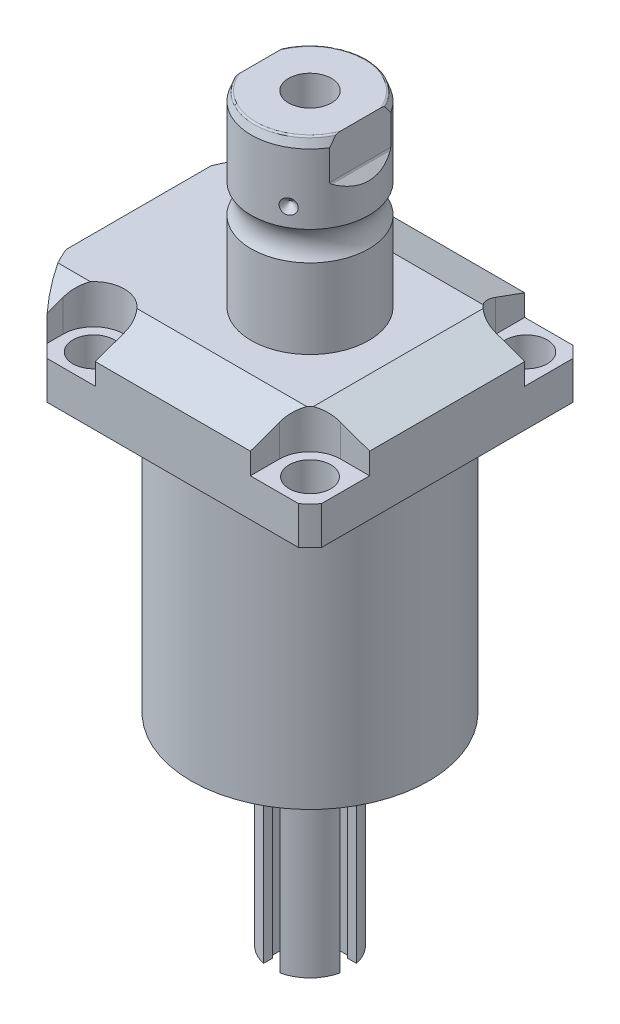
SolidWorks part; units mm, degrees
material "Alloy Steel"
ref_plane "Front Plane" through (0, 0, 0) normal (0, 0, 1) x (1, 0, 0)
ref_plane "Top Plane" through (0, 0, 0) normal (0, 1, 0) x (1, 0, 0)
ref_plane "Right Plane" through (0, 0, 0) normal (1, 0, 0) x (0, 0, -1)
ref_plane "Plane1" through (0, 0, 0) normal (0, 1, 0) x (0, 0, 1)
sketch "Sketch1" plane through (0, 0, 0) normal (0, 1, 0) x (0, 0, 1)
  line L0 (-44.45, 44.45) -> (44.45, 44.45)
  line L1 (44.45, 44.45) -> (44.45, -55.55)
  line L2 (44.45, -55.55) -> (-44.45, -55.55)
  line L3 (-44.45, -55.55) -> (-44.45, 44.45)
  line L4 (0, 0) -> (0, -60.6467) construction
  dimension "D1" = 55.55
  dimension "D2" = 100
  dimension "D3" = 88.9
extrude "Extrude1" add sketch "Sketch1" along normal blind 113.919
sketch "Sketch2" plane through (0, 0, 0) normal (0, -1, 0) x (1, 0, 0)
  circle A0 centre (0, 0) radius 60.325
  dimension "D1" = 120.65
extrude "Cut-Extrude1" cut sketch "Sketch2" against normal through all flip side to cut
ref_plane "Plane2" through (0, 0, 0) normal (1, 0, 0) x (0, 0, 1)
sketch "Sketch3" plane through (0, 0, 0) normal (1, 0, 0) x (0, 0, 1)
  line L0 (38.4935, 0) -> (38.4935, -88.9)
  line L1 (38.4935, -88.9) -> (76.5937, -88.9)
  line L2 (76.5937, -88.9) -> (76.5937, 0)
  line L3 (76.5937, 0) -> (38.4935, 0)
  line L4 (0, -93.345) -> (0, 4.445) construction
  line L5 (40.7836, 0) -> (-40.7836, 0) construction
  dimension "D1" = 76.987
  dimension "D2" = 153.1874
  dimension "D3" = 88.9
revolve "Cut-Revolve1" cut sketch "Sketch3" angle 360 about L4
fillet "Fillet1" radius 0.381 1 edges at (0, 88.9, 38.4935)
sketch "Sketch4" plane through (0, 113.919, 0) normal (0, 1, 0) x (-1, 0, 0)
  line L0 (-44.45, 40.7836) -> (-44.45, -40.7836) construction
  line L1 (40.7836, 44.45) -> (-40.7836, 44.45) construction
  line L2 (-25.121, -44.45) -> (-25.121, -35.052)
  line L3 (-44.45, -44.45) -> (-25.121, -44.45)
  line L4 (-44.45, -25.121) -> (-44.45, -44.45)
  line L5 (-35.052, -25.121) -> (-44.45, -25.121)
  line L6 (44.983, -44.45) -> (25.121, -44.45)
  line L7 (25.121, 44.45) -> (25.121, 35.052)
  line L8 (44.983, 44.45) -> (44.983, 35.052)
  line L9 (44.983, 44.45) -> (25.121, 44.45)
  line L10 (-35.052, 25.121) -> (-44.45, 25.121)
  line L11 (-44.45, 25.121) -> (-44.45, 44.45)
  line L12 (-44.45, 44.45) -> (-25.121, 44.45)
  line L13 (-25.121, 44.45) -> (-25.121, 35.052)
  line L14 (-48.9217, 0) -> (49.4551, 0) construction
  line L15 (44.983, -44.45) -> (44.983, -35.052)
  line L16 (25.121, -44.45) -> (25.121, -35.052)
  arc A0 (25.121, -35.052) -> (44.983, -35.052) centre (35.052, -35.052) cw
  arc A1 (-35.052, -25.121) -> (-25.121, -35.052) centre (-35.052, -35.052) cw
  arc A2 (-35.052, 25.121) -> (-25.121, 35.052) centre (-35.052, 35.052) ccw
  arc A3 (25.121, 35.052) -> (44.983, 35.052) centre (35.052, 35.052) ccw
  dimension "D2" = 9.931
  dimension "D1" = 35.052
  dimension "D3" = 35.052
  dimension "D4" = 35.052
extrude "Cut-Extrude2" cut sketch "Sketch4" against normal blind 12.7
ref_plane "Plane3" through (0, 0, 0) normal (1, 0, 0) x (0, 0, -1)
sketch "Sketch5" plane through (0, 0, 0) normal (1, 0, 0) x (0, 0, -1)
  line L0 (-28.575, 113.919) -> (-44.45, 108.141)
  line L1 (0, 0) -> (0, 154.1081) construction
  line L2 (-28.575, 113.919) -> (-44.45, 113.919)
  line L3 (-44.45, 113.919) -> (-44.45, 108.141)
  dimension "D1" = 15.875
  dimension "D2" = 20
extrude "Cut-Extrude9" cut sketch "Sketch5" against normal through all and the other way through all
mirror "Mirror1" about plane through (0, 0, 0) normal (0, 0, 1) of "Cut-Extrude9"
ref_plane "Plane7" through (0, 0, 0) normal (0, 0, 1) x (1, 0, 0)
sketch "Sketch9" plane through (0, 0, 0) normal (0, 0, 1) x (1, 0, 0)
  line L0 (28.575, 113.919) -> (44.45, 108.141)
  line L1 (44.45, 108.141) -> (44.45, 113.919)
  line L2 (44.45, 113.919) -> (28.575, 113.919)
  dimension "D1" = 15.875
  dimension "D2" = 20
extrude "Cut-Extrude7" cut sketch "Sketch9" against normal through all and the other way through all
ref_plane "Plane8" through (-41.402, 88.9, -18.1102) normal (1, 0, 0) x (0, 1, 0)
sketch "Sketch20" plane through (-41.402, 88.9, -18.1102) normal (1, 0, 0) x (0, 1, 0)
  line L0 (-88.9, 18.1102) -> (39.8401, 18.1102) construction
  line L1 (-7.2797, 36.2202) -> (36.9042, 36.2202) construction
  line L2 (0, 41.9225) -> (1.4478, 41.9225)
  line L3 (0, 58.8938) -> (0, -22.6734) construction
  line L4 (1.4478, 41.9225) -> (1.4478, 39.4714)
  line L5 (1.4478, 39.4714) -> (2.4638, 39.4714)
  line L6 (2.4638, 39.4714) -> (2.4638, 37.4648)
  line L7 (2.4638, 37.4648) -> (13.4366, 37.4648)
  line L8 (13.4366, 37.4648) -> (13.4366, 36.2202)
  line L9 (13.4366, 36.2202) -> (0, 36.2202)
  line L10 (0, 41.9225) -> (0, 36.2202)
  dimension "D1" = 18.11
  dimension "D2" = 11.4046
  dimension "D3" = 1.4478
  dimension "D4" = 6.5024
  dimension "D5" = 1.016
  dimension "D6" = 2.4892
  dimension "D7" = 10.9728
revolve "Cut-Revolve4" cut sketch "Sketch20" angle 360 about L1
mirror "Mirror10" about plane through (0, 0, 0) normal (0, 0, 1) of "Cut-Revolve4"
sketch "Sketch10" plane through (-41.402, 88.9, -18.1102) normal (1, 0, 0) x (0, 1, 0)
  line L0 (-1.0325, 0.0002) -> (1.5659, 0.0002) construction
  line L1 (13.4366, 1.2448) -> (2.4638, 1.2448) construction
  line L2 (2.4638, -1.2444) -> (13.4366, -1.2444) construction
  line L3 (0, 58.8938) -> (0, -22.6734) construction
  circle A0 centre (0.2667, 4.5214) radius 1.1811
  dimension "D1" = 2.3622
  dimension "D2" = 0.2667
  dimension "D3" = 9.0424
revolve "Revolve4" add sketch "Sketch10" angle 360 about L0
ref_plane "Plane9" through (-41.402, 88.9, 18.1102) normal (1, 0, 0) x (0, 1, 0)
sketch "Sketch11" plane through (-41.402, 88.9, 18.1102) normal (1, 0, 0) x (0, 1, 0)
  line L0 (-1.0325, -0.0002) -> (1.5659, -0.0002) construction
  line L1 (13.4366, 1.2444) -> (2.4638, 1.2444) construction
  line L3 (0, 22.6734) -> (0, -58.8938) construction
  line L4 (2.4638, -1.2448) -> (13.4366, -1.2448) construction
  circle A0 centre (0.2667, 4.521) radius 1.1811
  dimension "D1" = 2.3622
  dimension "D2" = 9.0424
  dimension "D3" = 0.2667
revolve "Revolve2" add sketch "Sketch11" angle 360 about L0
ref_plane "Plane10" through (-55.5498, 101.9048, 12.9794) normal (0, 0, 1) x (0, 1, 0)
sketch "S2D0007" plane through (-55.5498, 101.9048, 12.9794) normal (0, 0, 1) x (0, 1, 0)
  line L0 (0.0002, 0.0002) -> (10.7444, 0.0002)
  line L1 (10.7444, 0.0002) -> (10.7444, -0.2538)
  line L2 (10.7444, -0.2538) -> (6.655, -0.2538)
  line L3 (6.655, -0.2538) -> (5.9438, -0.965)
  line L5 (5.9438, -0.965) -> (5.9438, -14.427)
  line L6 (5.9438, -14.427) -> (0.0002, -14.427)
  line L7 (0.0002, -14.427) -> (0.0002, 0.0002)
  line L8 (0.0002, -14.9352) -> (0.0002, 0.7112) construction
  line L9 (-13.0048, 0.0002) -> (-13.0048, -14.7662) construction
  line L10 (12.0142, 0.0002) -> (-13.0048, 0.0002) construction
  dimension "D1" = 0.254
  dimension "D2" = 13.005
  dimension "D3" = 45
  dimension "D4" = 0.254
  dimension "D5" = 21.4884
  dimension "D6" = 13.3096
  dimension "D9" = 11.8872
  dimension "D10" = 14.1732
revolve "Cut-Revolve2" cut sketch "S2D0007" angle 360 about L8
pattern_linear "LPattern1" count 2 spacing 25.9588 along (0, 0, -1) of "Cut-Revolve2"
ref_plane "Plane12" through (0, 0, 0) normal (1, 0, 0) x (0, -1, 0)
sketch "Sketch15" plane through (0, 0, 0) normal (1, 0, 0) x (0, -1, 0)
  line L0 (-113.919, 0) -> (-113.919, 19.05)
  line L1 (-113.919, 19.05) -> (-139.6407, 19.05)
  line L2 (-149.0553, 19.05) -> (-171.602, 19.05)
  line L3 (-174.523, 17.9868) -> (-174.523, 0)
  line L4 (-174.523, 0) -> (-113.919, 0)
  line L5 (-197.6361, 0) -> (-64.6704, 0) construction
  line L6 (-113.919, 27.5238) -> (-113.919, -27.5238) construction
  line L8 (-174.523, 17.9868) -> (-171.602, 19.05)
  line L9 (0, -38.4935) -> (0, 38.4935) construction
  arc A0 (-149.0553, 19.05) -> (-139.6407, 19.05) centre (-144.348, 25.4255) ccw
  dimension "D2" = 20
  dimension "D4" = 7.925
  dimension "D6" = 35.001
  dimension "D1" = 174.523
  dimension "D3" = 38.1
  dimension "D5" = 30.175
  dimension "D7" = 2.921
revolve "Revolve3" add sketch "Sketch15" angle 360 about L5
ref_plane "Plane13" through (0, 0, 0) normal (0, 0, -1) x (0, -1, 0)
sketch "Sketch16" plane through (0, 0, 0) normal (0, 0, 1) x (0, -1, 0)
  line L0 (-174.523, 19.05) -> (-158.7389, 19.05)
  line L1 (-174.523, -19.05) -> (-174.523, -16.2815)
  line L2 (-174.523, 16.2815) -> (-161.823, 16.2815)
  line L3 (-161.2842, 16.5047) -> (-158.7389, 19.05)
  line L4 (-161.2842, -16.5047) -> (-158.7389, -19.05)
  line L5 (-174.523, -16.2815) -> (-161.823, -16.2815)
  line L6 (-174.523, 19.05) -> (-174.523, 16.2815)
  line L7 (-174.523, -19.05) -> (-158.7389, -19.05)
  line L8 (-194.0458, 0) -> (-125.0021, 0) construction
  line L11 (-174.523, 17.9868) -> (-174.523, -17.9868) construction
  line L12 (-149.0553, 19.05) -> (-171.602, 19.05) construction
  arc A0 (-161.823, 16.2815) -> (-161.2842, 16.5047) centre (-161.823, 17.0435) ccw
  arc A1 (-161.823, -16.2815) -> (-161.2842, -16.5047) centre (-161.823, -17.0435) cw
  point P3 (-161.5074, 16.2815)
  dimension "D4" = 0.762
  dimension "D1" = 32.563
  dimension "D2" = 45
  dimension "D3" = 12.7
extrude "Cut-Extrude8" cut sketch "Sketch16" against normal mid plane 106.68
hole_wizard "Hole1" positions "Sketch18" profile "Sketch17" legacy end condition up to next
sketch "Sketch18" plane through (0, 101.219, 0) normal (0, 1, 0) x (-1, 0, 0)
  arc A0 (44.983, -35.052) -> (25.121, -35.052) centre (35.052, -35.052) ccw construction
  arc A1 (25.121, 35.052) -> (44.983, 35.052) centre (35.052, 35.052) ccw construction
  arc A2 (-35.052, 25.121) -> (-25.121, 35.052) centre (-35.052, 35.052) ccw construction
  arc A3 (-25.121, -35.052) -> (-35.052, -25.121) centre (-35.052, -35.052) ccw construction
  point P0 (-35.052, -35.052)
  point P1 (-35.052, 35.052)
  point P3 (35.052, 35.052)
  point P5 (35.052, -35.052)
sketch "Sketch17" plane through (35.052, 101.219, -35.052) normal (1, 0, 0) x (0, 0, 1)
  line L0 (0, 0) -> (0, 12.319)
  line L1 (0, 12.319) -> (6.7435, 12.319)
  line L2 (6.7435, 12.319) -> (6.7435, 0)
  line L3 (6.7435, 0) -> (0, 0)
  line L4 (0, 110) -> (0, -10) construction
  dimension "Diameter" = 13.487
  dimension "Depth" = 12.319
chamfer "Chamfer1" distance 0.635 angle 45 2 edges at (-41.402, 91.3638, 16.8654) (-41.402, 91.3638, -16.8654)
sketch "Sketch21" plane through (0, 0, 0) normal (0, 0, 1) x (1, 0, 0)
  line L0 (0, 0) -> (0, 194.0957) construction
  line L1 (0, 144.9565) -> (6.9342, 149.123)
  line L2 (6.9342, 149.123) -> (6.9342, 174.523)
  line L4 (6.9342, 174.523) -> (0, 174.523)
  line L5 (0, 174.523) -> (0, 144.9565)
  line L6 (16.2815, 174.523) -> (-16.2815, 174.523) construction
  dimension "D1" = 13.8684
  dimension "D2" = 59
  dimension "D3" = 25.4
revolve "Cut-Revolve5" cut sketch "Sketch21" angle 360 about L0
fillet "Fillet2" radius 0.635 2 edges at (0, 174.523, -17.9868) (0, 174.523, 17.9868)
sketch "Sketch22" plane through (0, 0, 0) normal (0, 0, 1) x (1, 0, 0)
  line L0 (-37.9974, 155.016) -> (37.12, 155.016) construction
  line L1 (-19.05, 157.429) -> (-16.637, 155.016)
  line L2 (-16.637, 155.016) -> (-19.05, 155.016)
  line L3 (-19.05, 155.016) -> (-19.05, 157.429)
  arc A0 (-19.05, 139.6407) -> (-19.05, 149.0553) centre (-25.4255, 144.348) ccw construction
  dimension "D2" = 10.668
  dimension "D1" = 4.826
  dimension "D3" = 45
revolve "Cut-Revolve6" cut sketch "Sketch22" angle 360 about L0
pattern_circular "CirPattern1" count 3 over 360 about axis through (0, 197.6361, 0) along (0, 1, 0) of "Cut-Revolve6"
sketch "Sketch23" plane through (0, 0, 0) normal (0, 0, 1) x (1, 0, 0)
  line L0 (0, -970.2435) -> (0, 49029.7565) construction
  line L2 (0, 0) -> (-22.225, 0)
  line L3 (-38.4935, 0) -> (38.4935, 0) construction
  line L4 (-22.225, 0) -> (-22.225, -2.54)
  line L5 (-22.225, -2.54) -> (-12.7, -2.54)
  line L6 (-12.7, -2.54) -> (-12.7, -65.5321)
  line L7 (-12.7, -65.5321) -> (0, -65.5321)
  line L8 (0, -65.5321) -> (0, 0)
  dimension "D1" = 25.4001
  dimension "D2" = 65.5321
  dimension "D3" = 2.54
  dimension "D4" = 44.4501
revolve "Revolve5" add sketch "Sketch23" angle 360 about L0
sketch "Sketch24" plane through (0, -2.54, 0) normal (0, -1, 0) x (1, 0, 0)
  line L0 (-1000, 0) -> (49000, 0) construction
  line L2 (0, -1000) -> (0, 49000) construction
  line L3 (0, 0) -> (43301.2702, 25000) construction
  line L4 (0, 0) -> (25000, 43301.2702) construction
  circle A0 centre (0, 0) radius 19.431 construction
  circle A1 centre (19.431, 0) radius 1.7272
  circle A2 centre (16.8278, 9.7155) radius 1.7272
  circle A3 centre (9.7155, 16.8278) radius 1.7272
  circle A4 centre (0, 19.431) radius 1.7272
  circle A5 centre (-9.7155, 16.8278) radius 1.7272
  circle A6 centre (-16.8278, 9.7155) radius 1.7272
  circle A7 centre (-19.431, 0) radius 1.7272
  circle A8 centre (16.8278, -9.7155) radius 1.7272
  circle A9 centre (9.7155, -16.8278) radius 1.7272
  circle A10 centre (0, -19.431) radius 1.7272
  circle A11 centre (-9.7155, -16.8278) radius 1.7272
  circle A12 centre (-16.8278, -9.7155) radius 1.7272
  dimension "D3" = 38.8621
  dimension "D4" = 3.4544
  dimension "D5" = 3.4544
  dimension "D6" = 3.4544
  dimension "D7" = 3.4544
  dimension "D1" = 30
  dimension "D2" = 30
extrude "Cut-Extrude10" cut sketch "Sketch24" against normal up to surface (2.54 mm away) up to face at (0, 0, 38.4935)
sketch "Sketch25" plane through (0, -2.54, 0) normal (0, -1, 0) x (1, 0, 0)
  circle A0 centre (19.431, 0) radius 2.7051
  circle A1 centre (-9.7155, 16.8278) radius 2.7051
  circle A2 centre (-9.7155, -16.8278) radius 2.7051
  dimension "D1" = 5.4102
  dimension "D2" = 5.4102
  dimension "D3" = 5.4102
extrude "Extrude2" add sketch "Sketch25" along normal blind 2.9464
sketch "Sketch26" plane through (0, -5.4864, 0) normal (0, -1, 0) x (1, 0, 0)
  line L1 (-9.0153, -18.09) -> (-8.2724, -16.8525)
  line L2 (-8.2724, -16.8525) -> (-8.9725, -15.5903)
  line L3 (-8.9725, -15.5903) -> (-10.4157, -15.5656)
  line L4 (-10.4157, -15.5656) -> (-11.1587, -16.8031)
  line L5 (-11.1587, -16.8031) -> (-10.4585, -18.0652)
  line L6 (-10.4585, -18.0652) -> (-9.0153, -18.09)
  line L7 (19.9976, -1.3275) -> (20.864, -0.1731)
  line L8 (20.864, -0.1731) -> (20.2974, 1.1545)
  line L9 (20.2974, 1.1545) -> (18.8644, 1.3275)
  line L10 (18.8644, 1.3275) -> (17.9981, 0.1731)
  line L11 (17.9981, 0.1731) -> (18.5647, -1.1545)
  line L12 (18.5647, -1.1545) -> (19.9976, -1.3275)
  line L13 (-9.0392, 15.5527) -> (-8.2731, 16.776)
  line L14 (-8.2731, 16.776) -> (-8.9494, 18.0511)
  line L15 (-8.9494, 18.0511) -> (-10.3919, 18.1029)
  line L16 (-10.3919, 18.1029) -> (-11.158, 16.8796)
  line L17 (-11.158, 16.8796) -> (-10.4816, 15.6045)
  line L18 (-10.4816, 15.6045) -> (-9.0392, 15.5527)
  circle A0 centre (-9.7155, -16.8278) radius 1.25 construction
  circle A1 centre (19.431, 0) radius 1.25 construction
  circle A2 centre (-9.7155, 16.8278) radius 1.25 construction
  dimension "D1" = 2.5
  dimension "D2" = 2.5
  dimension "D3" = 2.5
extrude "Cut-Extrude11" cut sketch "Sketch26" against normal blind 2.032
ref_plane "Plane14-SLOT-ANGLE" through (0, 0, 0) normal (1, 0, 0) x (0, 0, -1)
ref_plane "Plane15" through (0, 0, 0) normal (0, 0, 1) x (1, 0, 0)
ref_plane "Plane16" through (0, -34.0361, 12.7) normal (0, 0, 1) x (-1, 0, 0)
sketch "Sketch27" plane through (0, -34.0361, 12.7) normal (0, 0, 1) x (-1, 0, 0)
  line L0 (0, -981.6708) -> (0, 49018.3292) construction
  line L2 (-2.6416, 31.4961) -> (-2.6416, -21.0834)
  line L3 (12.7, 31.4961) -> (-12.7, 31.4961) construction
  line L4 (-2.6416, 31.4961) -> (2.6416, 31.4961)
  line L5 (2.6416, 31.4961) -> (2.6416, -21.0834)
  arc A0 (-2.6416, -21.0834) -> (2.6416, -21.0834) centre (0, -23.368) ccw
  point P11 (0, 31.4961)
  dimension "D1" = 6.985
  dimension "D2" = 5.2832
  dimension "D3" = 54.8641
extrude "Cut-Extrude12" cut sketch "Sketch27" against normal blind 6.477
sketch "Sketch28" plane through (0, 0, 6.223) normal (0, 0, 1) x (1, 0, 0)
  line L0 (-1000, -10.668) -> (49000, -10.668) construction
  line L1 (0, -1010.668) -> (0, 48989.332) construction
  line L3 (3.4925, -65.5321) -> (3.4925, -10.668)
  line L4 (-12.7, -65.5321) -> (12.7, -65.5321) construction
  line L5 (3.4925, -10.668) -> (-3.4925, -10.668)
  line L6 (3.4925, -65.5321) -> (-3.4925, -65.5321)
  line L7 (-2.6416, -65.5321) -> (2.6416, -65.5321) construction
  line L8 (-3.4925, -65.5321) -> (-3.4925, -10.668)
  point P14 (0, -65.5321)
  point P15 (0, -10.668)
  dimension "D1" = 6.985
extrude "Cut-Extrude13" cut sketch "Sketch28" along normal blind 3.302
mirror "Mirror11" about plane through (0, 0, 0) normal (0, 0, 1) of "Cut-Extrude13", "Cut-Extrude12"
pattern_circular "CirPattern2" count 2 every 90 about axis through (0, 0, 0) along (0, 1, 0) of "Mirror11", "Cut-Extrude12", "Cut-Extrude13"
